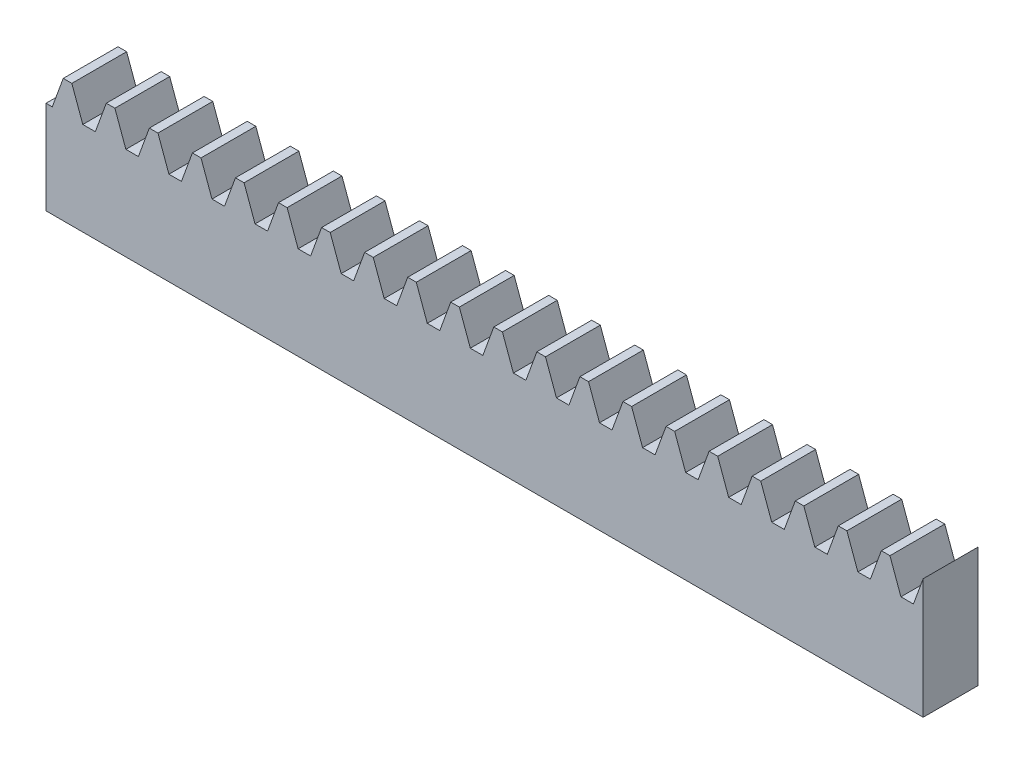
SolidWorks part; units mm, degrees
extrude "Blank" add sketch "BlankSke" against normal blind 3.175
sketch "BlankSke" plane through (0, 0, 0) normal (0, 0, 1) x (1, 0, 0)
  line L1 (0, 0) -> (50.8, 0)
  line L2 (0, 0) -> (0, 7.1437)
  line L3 (0, 7.1437) -> (50.8, 7.1437)
  line L4 (50.8, 0) -> (50.8, 7.1437)
  dimension "Blank_height" = 7.1437
ref_plane "Plane1" through (0, 0, 0) normal (0, 0, 1) x (1, 0, 0)
ref_plane "Plane2" through (0, 0, 0) normal (0, 1, 0) x (1, 0, 0)
ref_plane "Plane3" through (0, 0, 0) normal (1, 0, 0) x (0, 0, -1)
sketch "HoldingSke" plane through (0, 0, 0) normal (0, 1, 0) x (1, 0, 0)
  line L0 (0, 0) -> (622.6409, -522.4578)
  line L1 (-15, 0) -> (100, 0) construction
  line L2 (0, 0) -> (-2.1039, 2.3779)
  line L3 (0, 0) -> (-11.863, 4.5341)
  line L4 (0, 0) -> (8.0072, 3.2351)
  line L5 (0, 0) -> (-23.7986, -8.8762)
  line L6 (0, 0) -> (-10.5278, -7.1032)
  line L9 (-71.009, 38.7566) -> (-23.2726, 56.1312)
  line L10 (-76.2, 71.12) -> (-69.85, 71.12)
  line L11 (0, 0) -> (-3.175, 0)
  line L12 (-76.2, 101.6) -> (-76.1716, 101.6)
  line L13 (24.9733, 27.94) -> (52.9518, 28.4284)
  line L14 (24.9733, 27.94) -> (25.0241, 27.9398)
  line L15 (24.9733, 27.94) -> (100.4021, 29.52)
  circle A0 centre (0, 0) radius 19.05
  circle A1 centre (0, 0) radius 3.175
  circle A2 centre (0, 0) radius 12.7
  dimension "MPH" = 6.35
  dimension "Diameter" = 38.1
  dimension "Num_teeth" = 22
  dimension "Pitch" = 812.8
  dimension "Show_teeth" = 400
  dimension "Thickness" = 12.7
  dimension "Ap" = 20
  dimension "Pitch_height" = 6.35
  dimension "Width" = 3.175
  dimension "Backlash" = 0.0284
  dimension "Addendum_fac" = 1
  dimension "Dedendum_fac" = 1.2
  dimension "Clearance_fac" = 0.2
  dimension "Dedendum_add" = 0.0508
sketch "TooCutSkeIll" plane through (0, 0, 0) normal (0, 0, 1) x (1, 0, 0)
  line L0 (-0.9901, 7.1229) -> (-0.4123, 5.5354)
  line L1 (-0.2153, 5.3975) -> (0.2153, 5.3975)
  line L2 (0.4123, 5.5354) -> (0.9901, 7.1229)
  line L3 (50.8, 7.1437) -> (0, 7.1437) construction
  line L4 (0, 0) -> (0, 64.897) construction
  line L5 (-13.208, 6.35) -> (12.954, 6.35) construction
  line L6 (0, 0) -> (50.8, 0) construction
  line L7 (0.7088, 6.35) -> (0.7088, 48.7463) construction
  line L8 (-0.7088, 6.35) -> (-0.7088, 48.7463) construction
  line L9 (1.0199, 7.1437) -> (1.0199, 7.1692)
  line L10 (-1.0199, 7.1437) -> (-1.0199, 7.1692)
  line L11 (-1.0199, 7.1692) -> (1.0199, 7.1692)
  arc A0 (0.2153, 5.3975) -> (0.4123, 5.5354) centre (0.2153, 5.6071) ccw
  arc A1 (-0.4123, 5.5354) -> (-0.2153, 5.3975) centre (-0.2153, 5.6071) ccw
  arc A2 (1.0199, 7.1437) -> (0.9901, 7.1229) centre (1.0199, 7.112) ccw
  arc A3 (-0.9901, 7.1229) -> (-1.0199, 7.1437) centre (-1.0199, 7.112) ccw
  dimension "Pitch_height" = 6.35
  dimension "Addendum_plus" = 0.8192
  dimension "Pressure_angle" = 20
  dimension "Gap_width" = 1.4175
  dimension "Dedendum" = 0.9525
extrude "ToothCutIll" [suppressed] cut sketch "TooCutSkeIll" against normal through all
sketch "TooCutSkeSim" plane through (0, 0, 0) normal (0, 0, 1) x (1, 0, 0)
  line L0 (0.3621, 5.3975) -> (-0.3621, 5.3975)
  line L1 (1.0069, 7.1692) -> (0.3621, 5.3975)
  line L2 (0, 17.4625) -> (0, 53.467) construction
  line L3 (1.0069, 7.1692) -> (-1.0069, 7.1692)
  line L6 (-1.0069, 7.1692) -> (-0.3621, 5.3975)
  line L9 (-0.7088, 6.35) -> (0.7088, 6.35) construction
  line L10 (0, 0) -> (50.8, 0) construction
  line L11 (0.7088, 6.35) -> (0.7088, 53.467) construction
  line L12 (-0.7088, 6.35) -> (-0.7088, 53.467) construction
  dimension "Pitch_height" = 6.35
  dimension "Addendum_plus" = 0.8192
  dimension "Pressure_angle" = 20
  dimension "Gap_width" = 1.4175
  dimension "Dedendum" = 0.9525
extrude "ToothCutSim" cut sketch "TooCutSkeSim" against normal through all
pattern_linear "TeethCuts" count 21 spacing 2.4936 along (1, 0, 0) of "ToothCutIll", "ToothCutSim"
equation "' \"Pitch@HoldingSke\" = 4"
equation "' \"Num_teeth@HoldingSke\" = 12"
equation "' \"Ap@HoldingSke\" =  20"
equation "' \"Ap@HoldingSke\" = 20"
equation "' \"Width@HoldingSke\" = 0.25"
equation "' \"Show_teeth@HoldingSke\" = 500"
equation "' \"Backlash@HoldingSke\" = 0.009"
equation "' \"Addendum_fac@HoldingSke\" = 1.0"
equation "' \"Dedendum_fac@HoldingSke\" = 1.25"
equation "' \"Dedendum_add@HoldingSke\" = 0.00005"
equation "' \"Clearance_fac@HoldingSke\" = 0.25"
equation "' \"Pitch_height@HoldingSke\" = 1"
equation "' \"Length@HoldingSke\" = 4.71"
equation "\"MPH@HoldingSke\" = \"Dedendum_fac@HoldingSke\" / \"Pitch@HoldingSke\" + 2 * \"Dedendum_add@HoldingSke\" + 0.002"
equation "\"MPH@HoldingSke\" = ((sgn( \"MPH@HoldingSke\" - \"Pitch_height@HoldingSke\")+1)*( \"MPH@HoldingSke\" - \"Pitch_height@HoldingSke\"))/2 + \"Pitch_height@HoldingSke\""
equation "\"Blank_height@BlankSke\" = \"Pitch_height@HoldingSke\" + \"Addendum_fac@HoldingSke\"  / \"Pitch@HoldingSke\" "
equation "\"Length@BlankSke\" =  \"Length@HoldingSke\""
equation "\"Face_width@Blank\" = \"Width@HoldingSke\""
equation "\"Pressure_angle@TooCutSkeIll\" = \"Ap@HoldingSke\""
equation "\"Addendum_plus@TooCutSkeIll\" =  \"Addendum_fac@HoldingSke\"  / \"Pitch@HoldingSke\" + 0.001"
equation "\"Dedendum@TooCutSkeIll\" = \"Dedendum_fac@HoldingSke\"  / \"Pitch@HoldingSke\""
equation "\"Pitch_height@TooCutSkeIll\" =  \"MPH@HoldingSke\""
equation "\"Gap_width@TooCutSkeIll\" = 3.14159265 / 2 / \"Pitch@HoldingSke\" + 6 * \"Backlash@HoldingSke\""
equation "\"Pressure_angle@TooCutSkeSim\" = \"Ap@HoldingSke\""
equation "\"Addendum_plus@TooCutSkeSim\" =  \"Addendum_fac@HoldingSke\"  / \"Pitch@HoldingSke\" + 0.001"
equation "\"Dedendum@TooCutSkeSim\" = \"Dedendum_fac@HoldingSke\"  / \"Pitch@HoldingSke\""
equation "\"Pitch_height@TooCutSkeSim\" =  \"MPH@HoldingSke\""
equation "\"Gap_width@TooCutSkeSim\" = 3.14159265 / 2 / \"Pitch@HoldingSke\" + 6 * \"Backlash@HoldingSke\""
equation "\"Root_fillet@TooCutSkeIll\" = \"Clearance_fac@HoldingSke\" / \"Pitch@HoldingSke\" + \"Dedendum_add@HoldingSke\""
equation "\"Break_rad@TooCutSkeIll\" = 0.02 / \"Pitch@HoldingSke\" * 2"
equation "\"Linear_pitch@TeethCuts\" = 3.14159265 / \"Pitch@HoldingSke\""
equation "\"Num_teeth@HoldingSke\" = int( ( \"Length@HoldingSke\" + 0 ) / (3.14159265 / \"Pitch@HoldingSke\")) + 0.9999  + 1"
equation " \"Num_teeth@TeethCuts\" = int( \"Show_teeth@HoldingSke\" ) + 1"
equation " \"Num_teeth@TeethCuts\" = ((sgn( \"Num_teeth@TeethCuts\" - \"Num_teeth@HoldingSke\" )-1)*( \"Num_teeth@TeethCuts\" - \"Num_teeth@HoldingSke\" ))/-2+ \"Num_teeth@HoldingSke\""
equation " \"Num_teeth@TeethCuts\" = ((sgn( \"Num_teeth@TeethCuts\" - 2.0)+1)*( \"Num_teeth@TeethCuts\" - 2.0))/2 +2.0"
